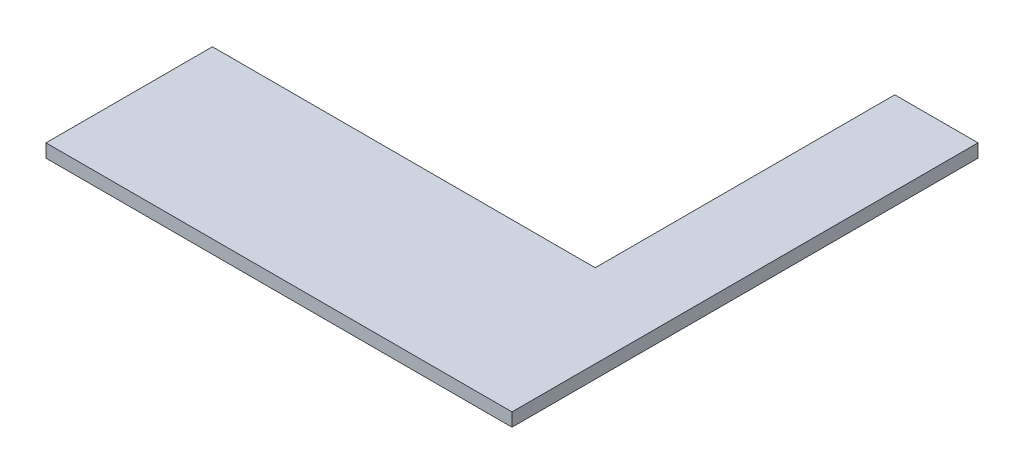
SolidWorks part; units mm, degrees
material "Maple"
ref_plane "Front Plane" through (0, 0, 0) normal (0, 0, 1) x (1, 0, 0)
ref_plane "Top Plane" through (0, 0, 0) normal (0, 1, 0) x (1, 0, 0)
ref_plane "Right Plane" through (0, 0, 0) normal (1, 0, 0) x (0, 0, -1)
sketch "Sketch1" plane through (0, 0, 0) normal (0, 1, 0) x (1, 0, 0)
  line L0 (0, 0) -> (-140, 0)
  line L1 (-140, 0) -> (-140, 50)
  line L2 (-140, 50) -> (-25, 50)
  line L3 (-25, 50) -> (-25, 140)
  line L4 (-25, 140) -> (0, 140)
  line L5 (0, 140) -> (0, 0)
  dimension "D1" = 140
  dimension "D2" = 140
  dimension "D3" = 25
  dimension "D4" = 50
extrude "Boss-Extrude1" add sketch "Sketch1" along normal blind 4
